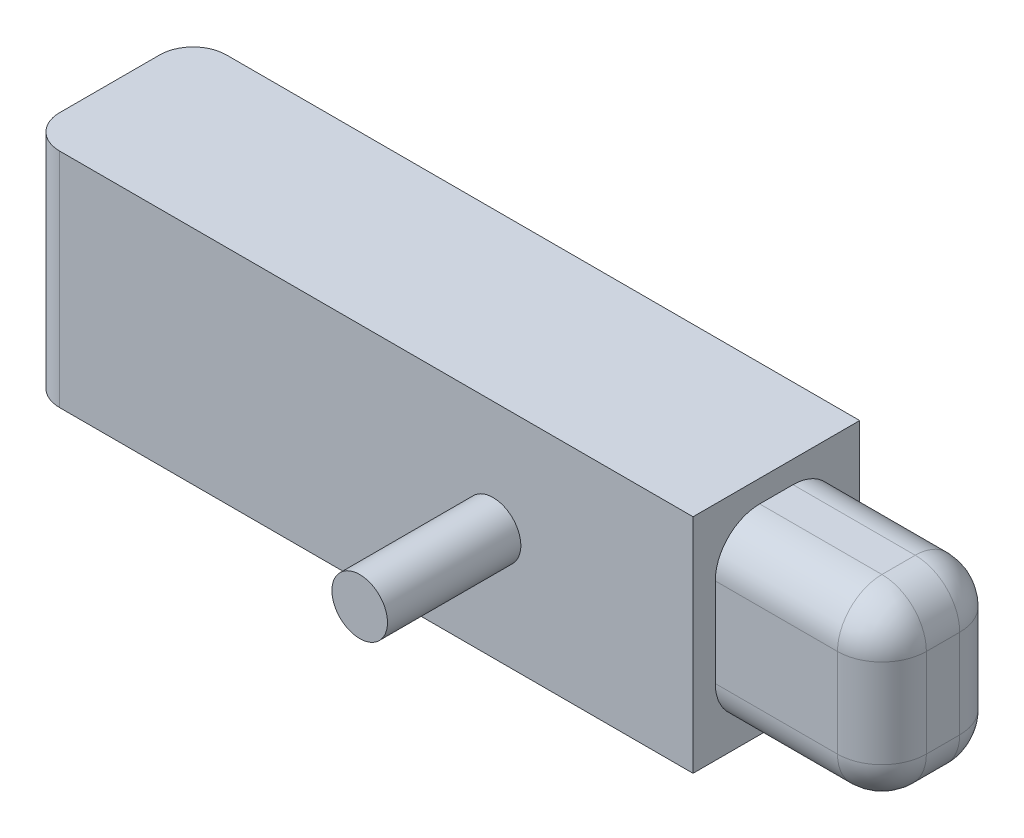
SolidWorks part; units mm, degrees
ref_plane "Alzado" through (0, 0, 0) normal (0, 0, 1) x (1, 0, 0)
ref_plane "Planta" through (0, 0, 0) normal (0, 1, 0) x (1, 0, 0)
ref_plane "Vista lateral" through (0, 0, 0) normal (1, 0, 0) x (0, 0, -1)
sketch "Croquis1" plane through (0, 0, 0) normal (0, 1, 0) x (1, 0, 0)
  line L1 (30, -7.5) -> (-30, -7.5)
  line L2 (30, -7.5) -> (30, 7.5)
  line L3 (30, 7.5) -> (-30, 7.5)
  line L4 (-30, -7.5) -> (-30, 7.5)
  line L5 (30, -7.5) -> (-30, 7.5) construction
  line L6 (30, 7.5) -> (-30, -7.5) construction
  point P0 (0, 0)
  dimension "D1" = 60
  dimension "D2" = 15
extrude "Saliente-Extruir1" add sketch "Croquis1" along normal blind 20
sketch "Croquis2" plane through (0, 0, 7.5) normal (0, 0, 1) x (1, 0, 0)
  line L0 (-30, 20) -> (-30, 0) construction
  line L1 (-30, 20) -> (30, 20) construction
  line L6 (30, 20) -> (30, 0) construction
  circle A0 centre (12, 10) radius 2.5
  point P6 (-30, 10)
  dimension "D1" = 5
  dimension "D2" = 18
  dimension "D3" = 10
extrude "Saliente-Extruir2" add sketch "Croquis2" along normal blind 12
sketch "Croquis3" plane through (30, 0, 0) normal (1, 0, 0) x (0, 0, -1)
  line L0 (-7.5, 20) -> (7.5, 20) construction
  line L1 (5.5, 2) -> (-5.5, 2)
  line L2 (5.5, 2) -> (5.5, 18)
  line L3 (5.5, 18) -> (-5.5, 18)
  line L4 (-5.5, 2) -> (-5.5, 18)
  line L5 (5.5, 2) -> (-5.5, 18) construction
  line L6 (5.5, 18) -> (-5.5, 2) construction
  line L7 (-7.5, 0) -> (7.5, 0) construction
  line L8 (-7.5, 20) -> (-7.5, 0) construction
  line L9 (7.5, 20) -> (7.5, 0) construction
  point P0 (0, 10)
  dimension "D1" = 2
  dimension "D2" = 2
  dimension "D3" = 2
  dimension "D4" = 2
extrude "Saliente-Extruir3" add sketch "Croquis3" along normal blind 15
fillet "Redondeo1" radius 4 4 edges at (37.5, 18, -5.5) (37.5, 2, -5.5) (37.5, 2, 5.5) (37.5, 18, 5.5)
fillet "Redondeo2" radius 4 8 edges at (45, 3.1716, -4.3284) (45, 2, 0) (45, 3.1716, 4.3284) (45, 10, 5.5) (45, 16.8284, 4.3284) (45, 18, 0) (45, 16.8284, -4.3284) (45, 10, -5.5)
fillet "Redondeo3" radius 3 2 edges at (-30, 10, -7.5) (-30, 10, 7.5)
scale "Escala1" scale about centroid uniform scaling yes scale factor 2
